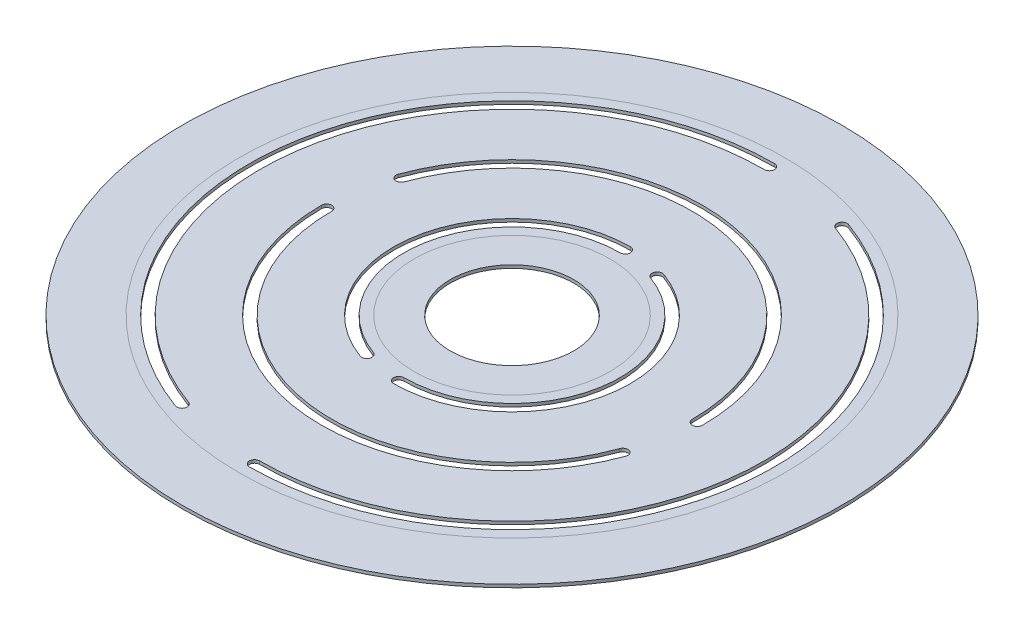
SolidWorks part; units mm, degrees
ref_plane "Front Plane" through (0, 0, 0) normal (0, 0, 1) x (1, 0, 0)
ref_plane "Top Plane" through (0, 0, 0) normal (0, 1, 0) x (1, 0, 0)
ref_plane "Right Plane" through (0, 0, 0) normal (1, 0, 0) x (0, 0, -1)
sketch "Sketch1" plane through (0, 0, 0) normal (0, 1, 0) x (1, 0, 0)
  line L0 (0, 32) -> (0, -32) construction
  line L1 (-32, 0) -> (32, 0) construction
  line L2 (-10.9446, -30.0702) -> (10.9446, 30.0702) construction
  line L3 (30.0702, -10.9446) -> (-30.0702, 10.9446) construction
  circle A0 centre (0, 0) radius 32
  circle A1 centre (0, 0) radius 6
  arc A2 (0, 11) -> (-3.7622, -10.3366) centre (0, 0) ccw
  arc A3 (-18, 0) -> (16.9145, -6.1564) centre (0, 0) ccw
  arc A4 (0, 25) -> (-8.5505, -23.4923) centre (0, 0) ccw
  arc A9 (18, 0) -> (-16.9145, 6.1564) centre (0, 0) ccw
  arc A11 (0, -25) -> (8.5505, 23.4923) centre (0, 0) ccw
  arc A12 (0, -11) -> (3.7622, 10.3366) centre (0, 0) ccw
  arc A16 (0, 25.5) -> (-8.7215, -23.9622) centre (0, 0) ccw
  arc A17 (18.5, 0) -> (-17.3843, 6.3274) centre (0, 0) ccw
  arc A18 (0, -25.5) -> (8.7215, 23.9622) centre (0, 0) ccw
  arc A19 (0, 11.5) -> (-3.9332, -10.8065) centre (0, 0) ccw
  arc A20 (0, -11.5) -> (3.9332, 10.8065) centre (0, 0) ccw
  arc A21 (-18.5, 0) -> (17.3843, -6.3274) centre (0, 0) ccw
  arc A26 (0, 24.5) -> (-8.3795, -23.0225) centre (0, 0) ccw
  arc A27 (17.5, 0) -> (-16.4446, 5.9854) centre (0, 0) ccw
  arc A28 (0, -24.5) -> (8.3795, 23.0225) centre (0, 0) ccw
  arc A29 (0, 10.5) -> (-3.5912, -9.8668) centre (0, 0) ccw
  arc A30 (0, -10.5) -> (3.5912, 9.8668) centre (0, 0) ccw
  arc A31 (-17.5, 0) -> (16.4446, -5.9854) centre (0, 0) ccw
  arc A39 (0, 25.5) -> (0, 24.5) centre (0, 25) cw
  arc A40 (-8.7215, -23.9622) -> (-8.3795, -23.0225) centre (-8.5505, -23.4923) ccw
  arc A41 (18.5, 0) -> (17.5, 0) centre (18, 0) cw
  arc A42 (-17.3843, 6.3274) -> (-16.4446, 5.9854) centre (-16.9145, 6.1564) ccw
  arc A43 (0, -25.5) -> (0, -24.5) centre (0, -25) cw
  arc A44 (8.7215, 23.9622) -> (8.3795, 23.0225) centre (8.5505, 23.4923) ccw
  arc A45 (0, 11.5) -> (0, 10.5) centre (0, 11) cw
  arc A46 (-3.9332, -10.8065) -> (-3.5912, -9.8668) centre (-3.7622, -10.3366) ccw
  arc A47 (0, -11.5) -> (0, -10.5) centre (0, -11) cw
  arc A48 (3.9332, 10.8065) -> (3.5912, 9.8668) centre (3.7622, 10.3366) ccw
  arc A49 (-18.5, 0) -> (-17.5, 0) centre (-18, 0) cw
  arc A50 (17.3843, -6.3274) -> (16.4446, -5.9854) centre (16.9145, -6.1564) ccw
  dimension "D1" = 64
  dimension "D2" = 12
  dimension "D3" = 22
  dimension "D4" = 36
  dimension "D5" = 50
  dimension "D8" = 20
  dimension "D9" = 20
  dimension "D10" = 0.5
  dimension "D11" = 0.5
extrude "Boss-Extrude1" add sketch "Sketch1" along normal blind 0.3
sketch "Sketch2" plane through (0, 0.3, 0) normal (0, 1, 0) x (1, 0, 0)
  circle A0 centre (0, 0) radius 9.5
  circle A1 centre (0, 0) radius 26.5
split line "Split Line1"
